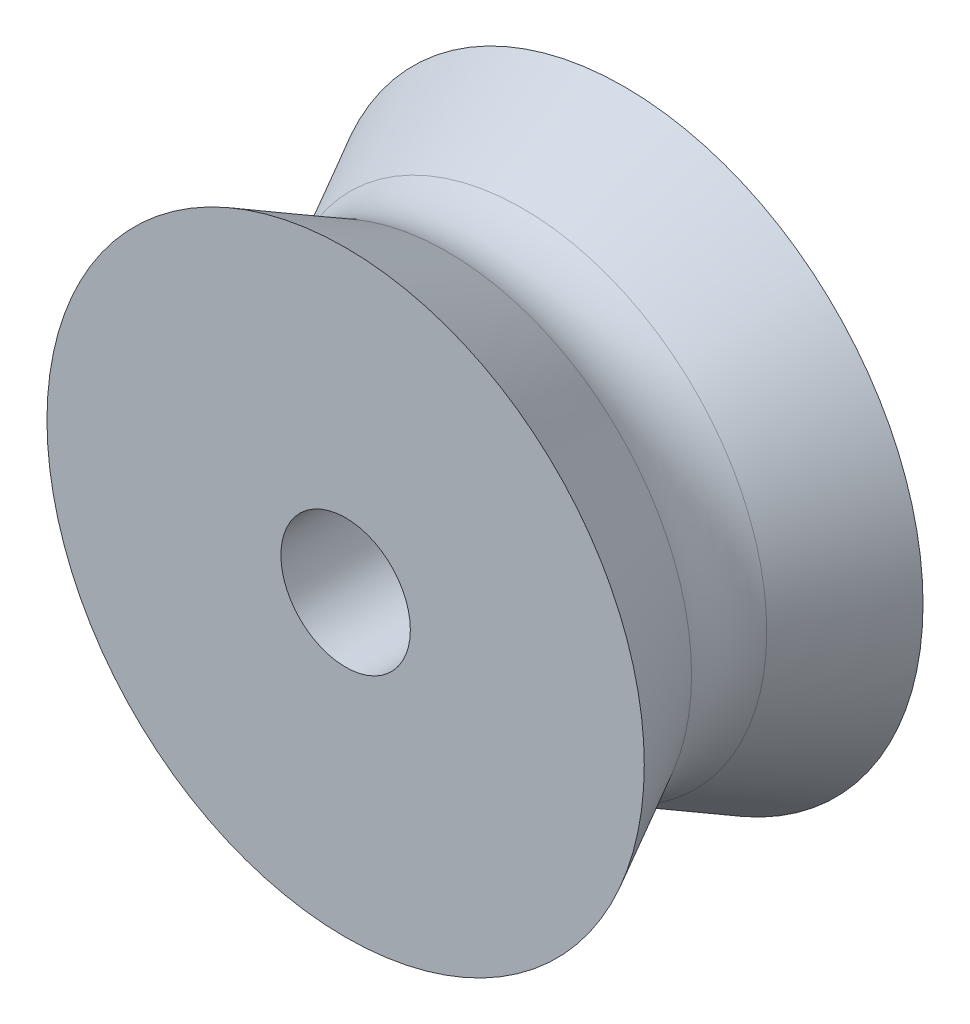
SolidWorks part; units mm, degrees
ref_plane "Front Plane" through (0, 0, 0) normal (0, 0, 1) x (1, 0, 0)
ref_plane "Top Plane" through (0, 0, 0) normal (0, 1, 0) x (1, 0, 0)
ref_plane "Right Plane" through (0, 0, 0) normal (1, 0, 0) x (0, 0, -1)
sketch "Sketch4" plane through (0, 0, 0) normal (0, 1, 0) x (1, 0, 0)
  line L0 (0, 0) -> (0, 22394.6975) construction
  line L1 (3.25, 0) -> (3.25, 14)
  line L2 (3.25, 14) -> (15, 14)
  line L3 (15, 14) -> (12.2619, 8.8889)
  line L4 (12.2619, 5.1111) -> (15, 0)
  line L5 (15, 0) -> (3.25, 0)
  arc A0 (12.2619, 8.8889) -> (12.2619, 5.1111) centre (15.7878, 7) ccw
  point P5 (15, 5)
  point P9 (12.98, 6.4302)
  point P10 (0, 0)
  point P11 (3.25, 7)
  point P14 (11.25, 7)
  dimension "D6" = 4
  dimension "D1" = 3.25
  dimension "D2" = 15
  dimension "D3" = 14
  dimension "D4" = 15
  dimension "D5" = 8
revolve "Revolve1" add sketch "Sketch4" angle 360 about L0
